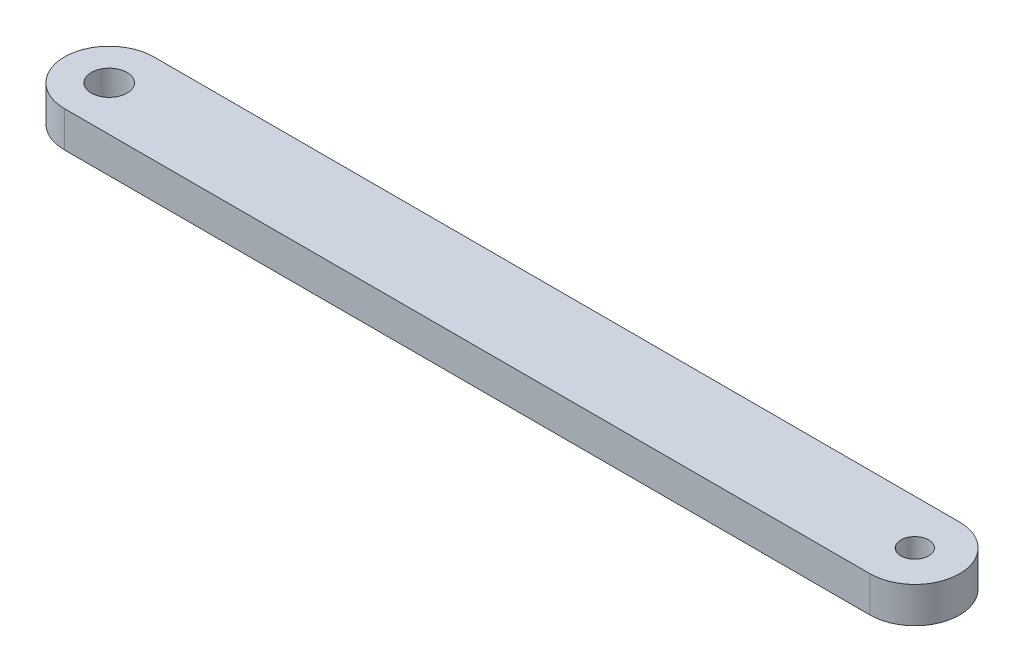
SolidWorks part; units mm, degrees
ref_plane "Front Plane" through (0, 0, 0) normal (0, 0, 1) x (1, 0, 0)
ref_plane "Top Plane" through (0, 0, 0) normal (0, 1, 0) x (1, 0, 0)
ref_plane "Right Plane" through (0, 0, 0) normal (1, 0, 0) x (0, 0, -1)
sketch "Sketch1" plane through (0, 0, 0) normal (0, 1, 0) x (1, 0, 0)
  line L0 (0, 0) -> (-90, 0) construction
  line L1 (0, -5) -> (-90, -5)
  line L2 (0, 5) -> (-90, 5)
  arc A0 (0, -5) -> (0, 5) centre (0, 0) ccw
  arc A1 (-90, 5) -> (-90, -5) centre (-90, 0) ccw
  circle A2 centre (-90, 0) radius 2
  circle A3 centre (0, 0) radius 1.55
  point P3 (-45, 0)
  dimension "D2" = 4
  dimension "D3" = 3.1
  dimension "D1" = 90
  dimension "D4" = 10
extrude "Boss-Extrude1" add sketch "Sketch1" along normal blind 4
